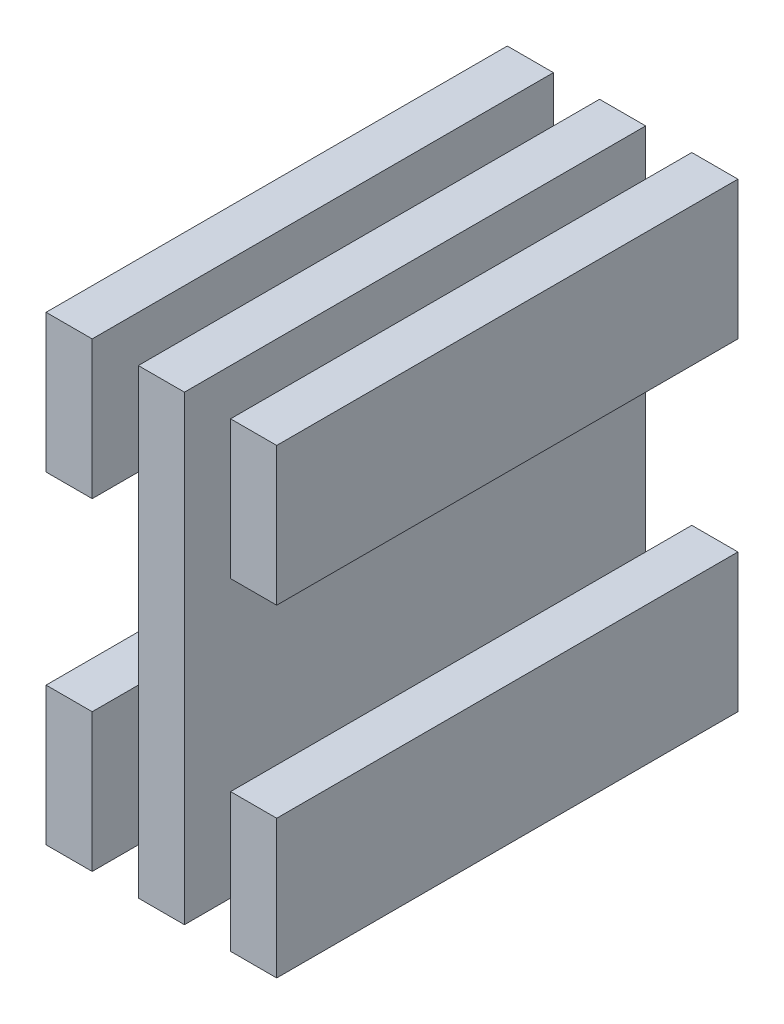
SolidWorks part; units mm, degrees
ref_plane "Front Plane" through (0, 0, 0) normal (0, 0, 1) x (1, 0, 0)
ref_plane "Top Plane" through (0, 0, 0) normal (0, 1, 0) x (1, 0, 0)
ref_plane "Right Plane" through (0, 0, 0) normal (1, 0, 0) x (0, 0, -1)
sketch "Sketch1" plane through (0, 0, 0) normal (0, 1, 0) x (1, 0, 0)
  line L0 (10, 50) -> (10, 0)
  line L1 (0, 50) -> (5, 50)
  line L2 (0, 50) -> (0, 0)
  line L3 (0, 0) -> (5, 0)
  line L4 (5, 50) -> (5, 0)
  line L5 (15, 50) -> (15, 0)
  line L6 (10, 50) -> (15, 50)
  line L7 (10, 0) -> (15, 0)
  line L8 (20, 50) -> (20, 0)
  line L9 (25, 50) -> (25, 0)
  line L10 (20, 50) -> (25, 50)
  line L11 (20, 0) -> (25, 0)
  dimension "D1" = 5
  dimension "D2" = 50
  dimension "D3" = 3
extrude "Boss-Extrude1" add sketch "Sketch1" along normal blind 50
sketch "Sketch2" plane through (25, 0, 0) normal (1, 0, 0) x (0, 0, -1)
  line L0 (0, 50) -> (50, 0) construction
  line L1 (0, 0) -> (50, 0) construction
  line L2 (50, 50) -> (0, 0) construction
  line L3 (50, 50) -> (50, 0) construction
  line L4 (0, 15) -> (50, 15)
  line L5 (0, 15) -> (0, 35)
  line L6 (0, 35) -> (50, 35)
  line L7 (50, 15) -> (50, 35)
  line L8 (0, 15) -> (50, 35) construction
  line L9 (0, 35) -> (50, 15) construction
  line L10 (0, 50) -> (0, 0) construction
  point P9 (25, 25)
  dimension "D1" = 20
extrude "Cut-Extrude1" cut sketch "Sketch2" against normal through all
